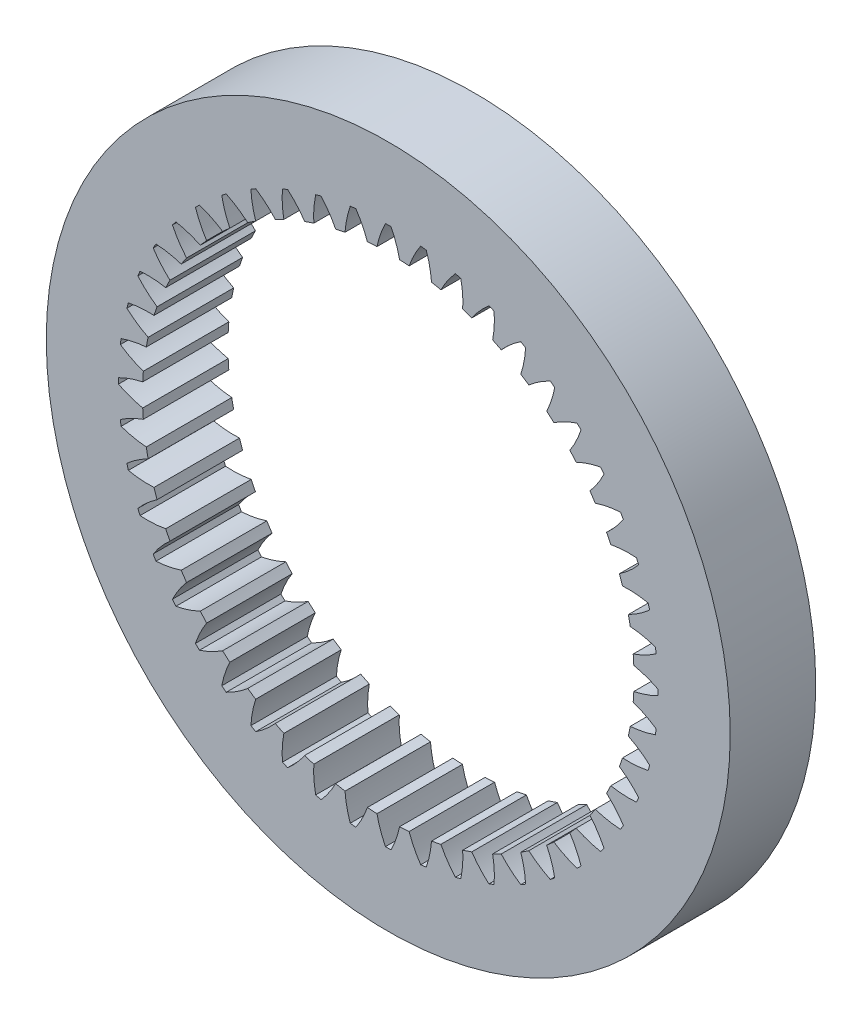
SolidWorks part; units mm, degrees
ref_plane "Front" through (0, 0, 0) normal (0, 0, 1) x (1, 0, 0)
ref_plane "Top" through (0, 0, 0) normal (0, 1, 0) x (1, 0, 0)
ref_plane "Right" through (0, 0, 0) normal (1, 0, 0) x (0, 0, -1)
sketch "Sketch2" plane through (0, 0, 0) normal (1, 0, 0) x (0, 0, -1)
  line L0 (0, 0) -> (-125.1835, 0) construction
  line L1 (-125.1835, 0) -> (0, 0) construction
ref_axis "Axis1" through (0, 0, -80.9) along (0, 0, 1)
sketch "gearSketch" plane through (0, 0, 0) normal (0, 0, 1) x (1, 0, 0)
  circle A0 centre (0, 0) radius 25.4
  dimension "bodyOD" = 50.8
extrude "gearBody" add sketch "gearSketch" along normal blind 6.35
sketch "boreSketch" plane through (0, 0, 0) normal (0, 0, -1) x (-1, 0, 0)
  circle A0 centre (0, 0) radius 18.2563
  dimension "minorDiameterBore" = 36.5125
extrude "bodyBore" cut sketch "boreSketch" against normal through all
sketch "toothCut1" plane through (-279.4, 0, 0) normal (0, 0, -1) x (-1, 0, 0)
  line L0 (-280.0233, 19.0398) -> (-273.0565, 16.7395) construction
  line L1 (-279.4, 0) -> (-279.4, 19.05) construction
  line L2 (-279.4, 0) -> (-280.0233, 19.0398) construction
  line L3 (-279.4, 279.4) -> (-279.4, 0) construction
  line L4 (-279.4, 0) -> (-280.2388, 18.237)
  line L5 (-279.4, 0) -> (-278.5612, 18.237)
  circle A0 centre (-279.4, 0) radius 18.2562 construction
  circle A1 centre (-279.4, 0) radius 17.9011 construction
  circle A2 centre (-279.4, 0) radius 19.05 construction
  arc A3 (-279.1916, 20.0411) -> (-279.6084, 20.0411) centre (-279.4, 0) ccw construction
  arc A4 (-279.1916, 20.0411) -> (-278.5612, 18.237) centre (-285.7435, 16.7395) cw
  arc A5 (-279.6084, 20.0411) -> (-280.2388, 18.237) centre (-273.0565, 16.7395) ccw
  arc A6 (-279.1916, 20.0411) -> (-279.6084, 20.0411) centre (-279.4, 0) ccw
  dimension "minorDiameter" = 36.5125
  dimension "baseDia" = 35.8023
  dimension "pd" = 38.1
  dimension "od" = 40.0844
  dimension "flankRadius2" = 7.3367
  dimension "toothAng" = 1.875
  dimension "flankRadius" = 7.3367
extrude "Cut-Extrude2" cut sketch "toothCut1" against normal through all
pattern_circular "CirPattern1" count 48 every 7.5 about axis through (0, 0, -80.9) along (0, 0, 1) of "Cut-Extrude2"
